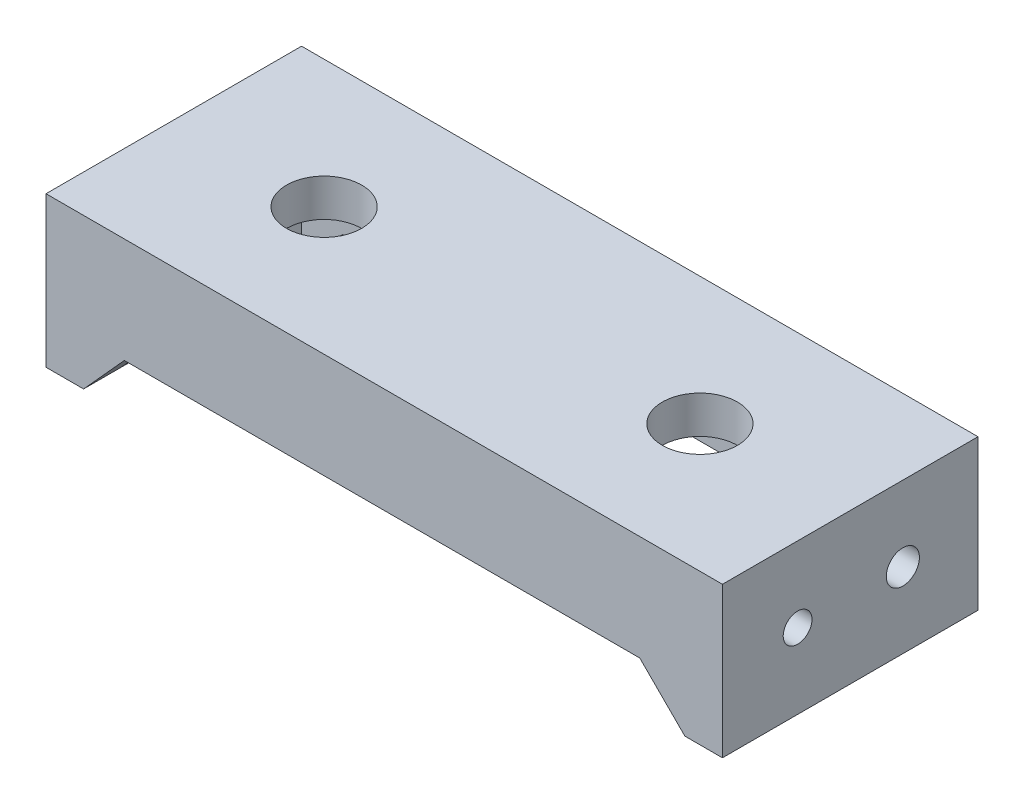
SolidWorks part; units mm, degrees
ref_plane "Front Plane" through (0, 0, 0) normal (0, 0, 1) x (1, 0, 0)
ref_plane "Top Plane" through (0, 0, 0) normal (0, 1, 0) x (1, 0, 0)
ref_plane "Right Plane" through (0, 0, 0) normal (1, 0, 0) x (0, 0, -1)
sketch "Sketch1" plane through (0, 0, 0) normal (0, 1, 0) x (1, 0, 0)
  line L1 (-22.5, 8.5) -> (22.5, 8.5)
  line L2 (-22.5, 8.5) -> (-22.5, -8.5)
  line L3 (-22.5, -8.5) -> (22.5, -8.5)
  line L4 (22.5, 8.5) -> (22.5, -8.5)
  line L5 (-22.5, 8.5) -> (22.5, -8.5) construction
  line L6 (-22.5, -8.5) -> (22.5, 8.5) construction
  point P0 (0, 0)
  dimension "D1" = 17
  dimension "D2" = 45
extrude "Boss-Extrude1" add sketch "Sketch1" along normal blind 2.5
sketch "Sketch2" plane through (0, 0, 0) normal (0, -1, 0) x (1, 0, 0)
  line L4 (-20, 6) -> (-20, -6)
  line L5 (-22.5, -8.5) -> (-22.5, 8.5)
  line L9 (20, 6) -> (20, -6)
  line L12 (-20, 6) -> (20, 6)
  line L14 (-22.5, -8.5) -> (22.5, -8.5)
  line L16 (-20, -6) -> (20, -6)
  line L18 (-22.5, 8.5) -> (22.5, 8.5)
  line L19 (22.5, 8.5) -> (22.5, -8.5)
extrude "Boss-Extrude2" add sketch "Sketch2" along normal blind 4.5
sketch "Sketch3" plane through (22.5, 0, 0) normal (1, 0, 0) x (0, 0, -1)
  line L0 (-8.5, 2.5) -> (8.5, 2.5) construction
  line L1 (-8.5, 2.5) -> (-8.5, -4.5) construction
  line L2 (8.5, 2.5) -> (8.5, -4.5) construction
  circle A0 centre (-3.5, -2.5) radius 0.9574
  circle A1 centre (3.5, -2.5) radius 1.1022
  dimension "D1" = 5
  dimension "D2" = 5
  dimension "D3" = 5
  dimension "D4" = 5
extrude "Cut-Extrude1" cut sketch "Sketch3" against normal through all
sketch "Sketch4" plane through (0, -4.5, 0) normal (0, -1, 0) x (1, 0, 0)
  line L0 (-22.5, -8.5) -> (22.5, -8.5) construction
  line L1 (-22.5, 8.5) -> (-20, 8.5)
  line L2 (-22.5, 8.5) -> (-22.5, -8.5)
  line L3 (-22.5, -8.5) -> (-20, -8.5)
  line L4 (-20, 8.5) -> (-20, -8.5)
  line L6 (22.5, 8.5) -> (20, 8.5)
  line L7 (22.5, 8.5) -> (22.5, -8.5)
  line L8 (22.5, -8.5) -> (20, -8.5)
  line L9 (20, 8.5) -> (20, -8.5)
  dimension "D1" = 2.5
  dimension "D2" = 2.5
extrude "Boss-Extrude3" add sketch "Sketch4" along normal blind 3
sketch "Sketch5" plane through (0, 0, 8.5) normal (0, 0, 1) x (1, 0, 0)
  line L0 (20, -7.5) -> (20, -4.5) construction
  line L1 (20, -7.5) -> (20, -4.5)
  line L2 (20, -4.5) -> (-20, -4.5) construction
  line L3 (20, -4.5) -> (17, -4.5)
  line L4 (20, -7.5) -> (17, -4.5)
  line L5 (-20, -7.5) -> (-20, -4.5) construction
  line L6 (-20, -7.5) -> (-20, -4.5)
  line L7 (-20, -7.5) -> (-17.2876, -4.5)
  line L8 (-17.2876, -4.5) -> (-20, -4.5)
  dimension "D1" = 3
  dimension "D2" = 3
extrude "Boss-Extrude4" add sketch "Sketch5" against normal up to surface (14.5 mm away)
sketch "Sketch6" plane through (0, 0, -8.5) normal (0, 0, -1) x (-1, 0, 0)
  line L0 (20, -4.5) -> (-20, -4.5) construction
  line L1 (20, -4.5) -> (17.2876, -4.5)
  line L2 (-17, -4.5) -> (-20, -4.5)
  line L6 (20, 0) -> (-20, 0)
  line L7 (-20, 0) -> (-20, -7.5)
  line L8 (-20, -7.5) -> (-17, -4.5)
  line L9 (-17, -4.5) -> (17.2876, -4.5)
  line L10 (17.2876, -4.5) -> (20, -7.5)
  line L11 (20, -7.5) -> (20, 0)
  line L13 (-20, -4.5) -> (-20, -7.5)
  line L14 (-20, -7.5) -> (-17, -4.5)
  line L16 (17.2876, -4.5) -> (20, -7.5)
  line L17 (20, -7.5) -> (20, -4.5)
  dimension "D1" = 0
extrude "Boss-Extrude5" add sketch "Sketch6" against normal up to surface (2.5 mm away) up to face at (0, -2.25, -6)
sketch "Sketch7" plane through (0, 2.5, 0) normal (0, 1, 0) x (1, 0, 0)
  line L0 (-22.5, 0) -> (22.5, 0) construction
  line L1 (-22.5, 8.5) -> (-22.5, -8.5) construction
  line L2 (22.5, -8.5) -> (22.5, 8.5) construction
  circle A0 centre (-12.5, 0) radius 2.5
  circle A1 centre (12.5, 0) radius 2.5
  dimension "D1" = 5
  dimension "D2" = 5
  dimension "D3" = 10
  dimension "D4" = 10
extrude "Cut-Extrude2" cut sketch "Sketch7" against normal up to surface (2.5 mm away) up to face at (0, 0, 0)
mirror "Mirror1" about plane through (0, 0, 0) normal (0, 0, 1)
